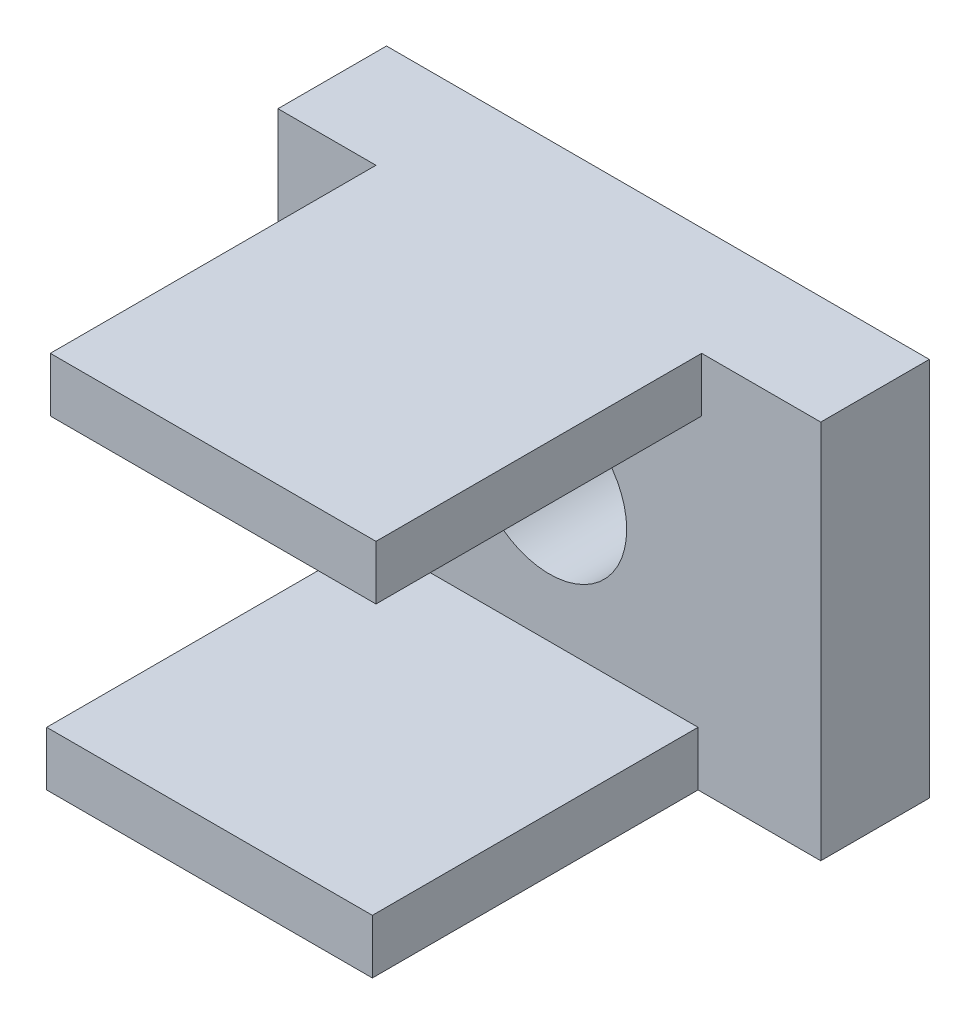
SolidWorks part; units mm, degrees
ref_plane "Front Plane" through (0, 0, 0) normal (0, 0, 1) x (1, 0, 0)
ref_plane "Top Plane" through (0, 0, 0) normal (0, 1, 0) x (1, 0, 0)
ref_plane "Right Plane" through (0, 0, 0) normal (1, 0, 0) x (0, 0, -1)
sketch "Sketch1" plane through (0, 0, 0) normal (0, 0, 1) x (1, 0, 0)
  line L1 (-5, 3.5) -> (5, 3.5)
  line L2 (-5, 3.5) -> (-5, -3.5)
  line L3 (-5, -3.5) -> (5, -3.5)
  line L4 (5, 3.5) -> (5, -3.5)
  line L5 (-5, 3.5) -> (5, -3.5) construction
  line L6 (-5, -3.5) -> (5, 3.5) construction
  point P0 (0, 0)
  dimension "D1" = 7
  dimension "D2" = 10
extrude "Boss-Extrude1" add sketch "Sketch1" along normal blind 2
sketch "Sketch2" plane through (0, 0, 2) normal (0, 0, 1) x (1, 0, 0)
  line L0 (5, 3.5) -> (-5, 3.5) construction
  line L1 (-3.1939, 2.5) -> (2.8061, 2.5)
  line L2 (-3.1939, 2.5) -> (-3.1939, 3.5)
  line L3 (-3.1939, 3.5) -> (2.8061, 3.5)
  line L4 (2.8061, 2.5) -> (2.8061, 3.5)
  line L5 (-3.1939, 2.5) -> (2.8061, 3.5) construction
  line L6 (-3.1939, 3.5) -> (2.8061, 2.5) construction
  line L7 (-5, -3.5) -> (5, -3.5) construction
  line L8 (-3.2605, -2.5) -> (2.7395, -2.5)
  line L9 (-3.2605, -2.5) -> (-3.2605, -3.5)
  line L10 (-3.2605, -3.5) -> (2.7395, -3.5)
  line L11 (2.7395, -2.5) -> (2.7395, -3.5)
  line L12 (-3.2605, -2.5) -> (2.7395, -3.5) construction
  line L13 (-3.2605, -3.5) -> (2.7395, -2.5) construction
  point P0 (-0.1939, 3)
  point P7 (-0.2605, -3)
  dimension "D1" = 1
  dimension "D2" = 6
  dimension "D3" = 1
  dimension "D4" = 6
extrude "Boss-Extrude2" add sketch "Sketch2" along normal blind 6
sketch "Sketch3" plane through (0, 0, 2) normal (0, 0, 1) x (1, 0, 0)
  circle A0 centre (0, 0) radius 1.425
  dimension "D1" = 2.85
extrude "Cut-Extrude1" cut sketch "Sketch3" against normal blind 6
